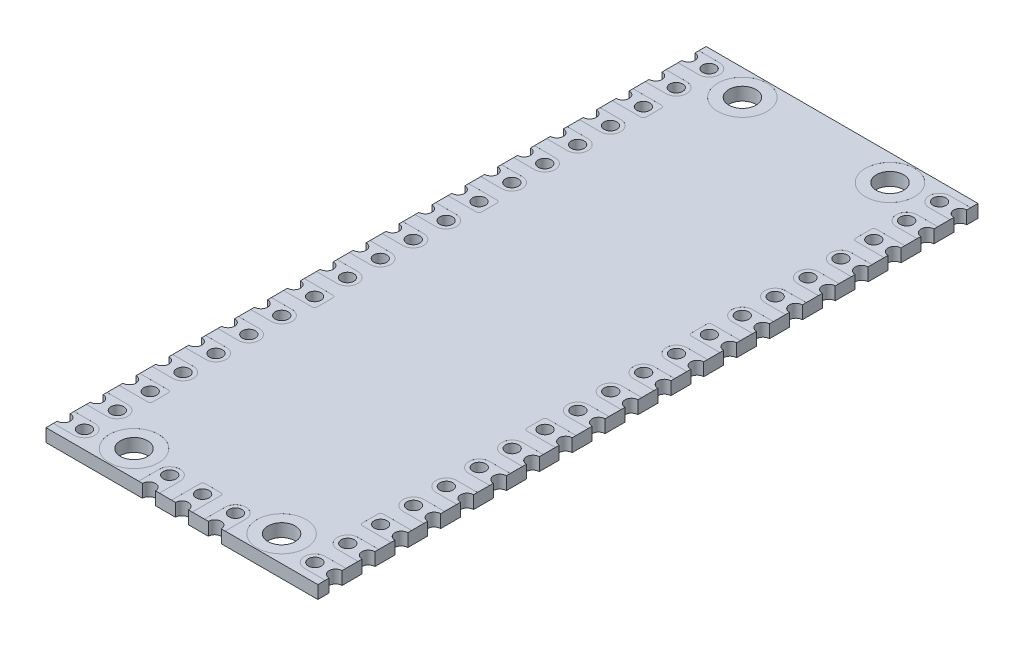
SolidWorks part; units mm, degrees
material "Power Circuit Board"
ref_plane "Front Plane" through (0, 0, 0) normal (0, 0, 1) x (1, 0, 0)
ref_plane "Top Plane" through (0, 0, 0) normal (0, 1, 0) x (1, 0, 0)
ref_plane "Right Plane" through (0, 0, 0) normal (1, 0, 0) x (0, 0, -1)
sketch "BaseS" plane through (0, 0, 0) normal (0, 1, 0) x (1, 0, 0)
  line L1 (-10.5, 25.5) -> (10.5, 25.5)
  line L2 (-10.5, 25.5) -> (-10.5, -25.5)
  line L3 (-10.5, -25.5) -> (10.5, -25.5)
  line L4 (10.5, 25.5) -> (10.5, -25.5)
  line L5 (-10.5, 25.5) -> (10.5, -25.5) construction
  line L6 (-10.5, -25.5) -> (10.5, 25.5) construction
  point P0 (0, 0)
  dimension "Width" = 21
  dimension "Length" = 51
extrude "Base" add sketch "BaseS" against normal mid plane 1
hole_wizard "Ø1.0 (1) Diameter Hole1" positions "Sketch2" profile "Sketch3" hole size "Ø1.0" standard "ANSI Metric" end condition through all
sketch "Sketch2" plane through (0, 0.5, 0) normal (0, 1, 0) x (1, 0, 0)
  line L0 (-10.5, 25.5) -> (-10.5, -25.5) construction
  line L1 (-10.5, -25.5) -> (10.5, -25.5) construction
  point P0 (-8.9, -24.13)
  dimension "XDim" = 1.6
  dimension "YDim" = 1.37
sketch "Sketch3" plane through (-8.9, 0.5, 24.13) normal (1, 0, 0) x (0, 0, 1)
  line L0 (0, 0) -> (0, 1)
  line L1 (0, 1) -> (0.5, 1)
  line L2 (0.5, 1) -> (0.5, 0)
  line L5 (0.5, 0) -> (0, 0)
  line L11 (0, -6.35) -> (0, 107.95) construction
  dimension "Thru Hole Dia." = 1
  dimension "Thru Hole Depth" = 1
pattern_linear "HoleHorzLP" count 2 spacing 1.6 along (1, 0, 0) of "Ø1.0 (1) Diameter Hole1"
sketch "SlotCutS" plane through (0, 0.5, 0) normal (0, 1, 0) x (1, 0, 0)
  line L0 (-8.9, -24.13) -> (-10.5, -24.13) construction
  line L1 (-8.9, -24.93) -> (-10.5, -24.93)
  line L2 (-8.9, -23.33) -> (-10.5, -23.33)
  arc A0 (-8.9, -24.93) -> (-8.9, -23.33) centre (-8.9, -24.13) ccw
  arc A1 (-10.5, -23.33) -> (-10.5, -24.93) centre (-10.5, -24.13) ccw
  circle A2 centre (-8.9, -24.13) radius 0.5 construction
  point P4 (-9.7, -24.13)
  dimension "RefDia" = 0.8
  dimension "DiaControl" = 0.3
extrude "SlotCut" cut sketch "SlotCutS" against normal blind 0.001
pattern_linear "HoleHorzLPSlotLP" count 20 spacing 2.54 along (0, 0, -1) of "Ø1.0 (1) Diameter Hole1", "HoleHorzLP", "SlotCut"
mirror "SHLPHM" about plane through (0, 0, 0) normal (1, 0, 0) of "Ø1.0 (1) Diameter Hole1", "HoleHorzLPSlotLP", "HoleHorzLP", "SlotCut"
hole_wizard "Ø2.1 (2.1) Diameter Hole1" positions "Sketch5" profile "Sketch6" hole size "Ø2.1" standard "ANSI Metric" end condition through all
sketch "Sketch5" plane through (0, 0.5, 0) normal (0, 1, 0) x (1, 0, 0)
  line L0 (-10.5, -25.5) -> (10.5, -25.5) construction
  line L1 (-10.5, -24.93) -> (-10.5, -25.5) construction
  point P0 (-5.7, -23.5)
  dimension "YDim" = 2
  dimension "XDim" = 4.8
sketch "Sketch6" plane through (-5.7, 0.5, 23.5) normal (1, 0, 0) x (0, 0, 1)
  line L0 (0, 0) -> (0, 1)
  line L1 (0, 1) -> (1.05, 1)
  line L2 (1.05, 1) -> (1.05, 0)
  line L5 (1.05, 0) -> (0, 0)
  line L11 (0, -6.35) -> (0, 107.95) construction
  dimension "Thru Hole Dia." = 2.1
  dimension "Thru Hole Depth" = 1
sketch "Soldering2.1mmHoleCutoutS" plane through (0, 0.5, 0) normal (0, 1, 0) x (1, 0, 0)
  circle A0 centre (-5.7, -23.5) radius 1.9
  circle A1 centre (-5.7, -23.5) radius 1.05 construction
  dimension "RefDia" = 3.8
  dimension "DiaControl" = 0.85
extrude "Soldering2.1mmHoleCutout" cut sketch "Soldering2.1mmHoleCutoutS" against normal up to surface (0.001 mm away) up to face at (-9.75, 0.499, 24.13)
mirror "SHCHM" about plane through (0, 0, 0) normal (1, 0, 0) of "Ø2.1 (2.1) Diameter Hole1", "Soldering2.1mmHoleCutout"
mirror "SHCHMVM" about plane through (0, 0, 0) normal (0, 0, 1) of "SHCHM", "Soldering2.1mmHoleCutout", "Ø2.1 (2.1) Diameter Hole1"
mirror "SHCTopVM" about plane through (0, 0, 0) normal (0, 1, 0) of "SHCHMVM", "SHCHM", "Soldering2.1mmHoleCutout"
sketch "SquareEtchS" plane through (0, 0.5, 0) normal (0, 1, 0) x (1, 0, 0)
  line L0 (-10.5, -19.85) -> (-10.5, -20.79) construction
  line L1 (-10.5, -18.25) -> (-8.3, -18.25)
  line L2 (-10.5, -18.25) -> (-10.5, -19.85)
  line L3 (-10.5, -19.85) -> (-8.3, -19.85)
  line L4 (-8.1, -18.45) -> (-8.1, -19.65)
  line L5 (-10.5, -19.85) -> (-8.9, -19.85) construction
  arc A0 (-8.9, -19.85) -> (-8.9, -18.25) centre (-8.9, -19.05) ccw construction
  arc A1 (-8.3, -19.85) -> (-8.1, -19.65) centre (-8.3, -19.65) ccw
  arc A2 (-8.1, -18.45) -> (-8.3, -18.25) centre (-8.3, -18.45) ccw
  dimension "Radius" = 0.2
extrude "SquareEtch" cut sketch "SquareEtchS" against normal up to surface (0.001 mm away) up to face at (-9.75, 0.499, 19.05)
pattern_linear "SELP" count 4 spacing 12.7 along (0, 0, -1) of "SquareEtch"
mirror "SELPHM" about plane through (0, 0, 0) normal (1, 0, 0) of "SELP", "SquareEtch"
hole_wizard "Ø1.0 (1) Diameter Hole2" positions "Sketch9" profile "Sketch10" hole size "Ø1.0" standard "ANSI Metric" end condition through all
sketch "Sketch9" plane through (0, 0.5, 0) normal (0, 1, 0) x (1, 0, 0)
  line L0 (0, -25.5) -> (0, -23.9) construction
  line L1 (-10.5, -25.5) -> (10.5, -25.5) construction
  point P0 (0, -23.9)
  dimension "YDim" = 1.6
sketch "Sketch10" plane through (0, 0.5, 23.9) normal (1, 0, 0) x (0, 0, 1)
  line L0 (0, 0) -> (0, 1)
  line L1 (0, 1) -> (0.5, 1)
  line L2 (0.5, 1) -> (0.5, 0)
  line L5 (0.5, 0) -> (0, 0)
  line L11 (0, -6.35) -> (0, 107.95) construction
  dimension "Thru Hole Dia." = 1
  dimension "Thru Hole Depth" = 1
sketch "VerticalSlotCutS" plane through (0, 0.5, 0) normal (0, 1, 0) x (1, 0, 0)
  line L0 (0, -23.9) -> (0, -25.5) construction
  line L1 (-10.5, -25.5) -> (10.5, -25.5) construction
  line L2 (0.8, -23.9) -> (0.8, -25.5)
  line L3 (-0.8, -23.9) -> (-0.8, -25.5)
  line L4 (-8.9, -24.13) -> (-10.5, -24.13) construction
  arc A0 (0.8, -23.9) -> (-0.8, -23.9) centre (0, -23.9) ccw
  arc A1 (-0.8, -25.5) -> (0.8, -25.5) centre (0, -25.5) ccw
  arc A2 (-8.9, -24.93) -> (-8.9, -23.33) centre (-8.9, -24.13) ccw construction
  point P4 (0, -24.7)
extrude "VerticalSlotCut" cut sketch "VerticalSlotCutS" against normal up to surface (0.999 mm away)
pattern_linear "DH2LP" count 2 spacing 1.6 along (0, 0, 1) of "Ø1.0 (1) Diameter Hole2"
pattern_linear "VSCHLP" count 2 spacing 2.54 along (1, 0, 0) count 2 spacing 2.54 along (-1, 0, 0) of "VerticalSlotCut", "Ø1.0 (1) Diameter Hole2", "DH2LP"
sketch "VerticalSquareEtchS" plane through (0, 0.5, 0) normal (0, 1, 0) x (1, 0, 0)
  line L0 (-1.74, -25.5) -> (-0.8, -25.5) construction
  line L1 (-0.6, -23.1) -> (0.6, -23.1)
  line L2 (-0.8, -23.3) -> (-0.8, -25.5)
  line L3 (-0.8, -25.5) -> (0.8, -25.5)
  line L4 (0.8, -23.3) -> (0.8, -25.5)
  line L5 (-0.8, -23.9) -> (-0.8, -25.5) construction
  arc A0 (0.8, -23.9) -> (-0.8, -23.9) centre (0, -23.9) ccw construction
  arc A1 (0.8, -23.3) -> (0.6, -23.1) centre (0.6, -23.3) ccw
  arc A2 (-0.6, -23.1) -> (-0.8, -23.3) centre (-0.6, -23.3) ccw
  arc A3 (-8.3, -19.85) -> (-8.1, -19.65) centre (-8.3, -19.65) ccw construction
extrude "VerticalSquareEtch" cut sketch "VerticalSquareEtchS" against normal up to surface (0.001 mm away)
sketch "VSCHPVMS" plane through (0, -0.5, 0) normal (0, -1, 0) x (1, 0, 0)
  line L0 (3.04, 25.5) -> (3.34, 25.5) construction
  line L1 (3.34, 25.5) -> (3.34, 23.9) construction
  line L2 (1.74, 23.9) -> (1.74, 25.5) construction
  line L3 (1.74, 25.5) -> (2.04, 25.5) construction
  line L4 (-2.04, 25.5) -> (-1.74, 25.5) construction
  line L5 (-1.74, 25.5) -> (-1.74, 23.9) construction
  line L6 (-3.34, 23.9) -> (-3.34, 25.5) construction
  line L7 (-3.34, 25.5) -> (-3.04, 25.5) construction
  line L8 (0.5, 25.5) -> (0.8, 25.5) construction
  line L9 (0.8, 25.5) -> (0.8, 23.3) construction
  line L10 (0.6, 23.1) -> (-0.6, 23.1) construction
  line L11 (-0.8, 23.3) -> (-0.8, 25.5) construction
  line L12 (-0.8, 25.5) -> (-0.5, 25.5) construction
  line L13 (3.04, 25.5) -> (3.34, 25.5)
  line L14 (3.34, 25.5) -> (3.34, 23.9)
  line L15 (1.74, 23.9) -> (1.74, 25.5)
  line L16 (1.74, 25.5) -> (2.04, 25.5)
  line L17 (-2.04, 25.5) -> (-1.74, 25.5)
  line L18 (-1.74, 25.5) -> (-1.74, 23.9)
  line L19 (-3.34, 23.9) -> (-3.34, 25.5)
  line L20 (-3.34, 25.5) -> (-3.04, 25.5)
  line L21 (0.5, 25.5) -> (0.8, 25.5)
  line L22 (0.8, 25.5) -> (0.8, 23.3)
  line L23 (0.6, 23.1) -> (-0.6, 23.1)
  line L24 (-0.8, 23.3) -> (-0.8, 25.5)
  line L25 (-0.8, 25.5) -> (-0.5, 25.5)
  arc A0 (2.04, 25.5) -> (3.04, 25.5) centre (2.54, 25.5) ccw construction
  arc A1 (1.74, 23.9) -> (3.34, 23.9) centre (2.54, 23.9) ccw construction
  arc A2 (-3.04, 25.5) -> (-2.04, 25.5) centre (-2.54, 25.5) ccw construction
  arc A3 (-3.34, 23.9) -> (-1.74, 23.9) centre (-2.54, 23.9) ccw construction
  arc A4 (-0.5, 25.5) -> (0.5, 25.5) centre (0, 25.5) ccw construction
  arc A5 (0.6, 23.1) -> (0.8, 23.3) centre (0.6, 23.3) ccw construction
  arc A6 (-0.8, 23.3) -> (-0.6, 23.1) centre (-0.6, 23.3) ccw construction
  arc A7 (2.04, 25.5) -> (3.04, 25.5) centre (2.54, 25.5) ccw
  arc A8 (1.74, 23.9) -> (3.34, 23.9) centre (2.54, 23.9) ccw
  arc A9 (-3.04, 25.5) -> (-2.04, 25.5) centre (-2.54, 25.5) ccw
  arc A10 (-3.34, 23.9) -> (-1.74, 23.9) centre (-2.54, 23.9) ccw
  arc A11 (-0.5, 25.5) -> (0.5, 25.5) centre (0, 25.5) ccw
  arc A12 (0.6, 23.1) -> (0.8, 23.3) centre (0.6, 23.3) ccw
  arc A13 (-0.8, 23.3) -> (-0.6, 23.1) centre (-0.6, 23.3) ccw
extrude "VSCHPVM" cut sketch "VSCHPVMS" against normal blind 0.001
equation "\"Depth@VSCHPVM\"=\"Depth@SlotCut\""
